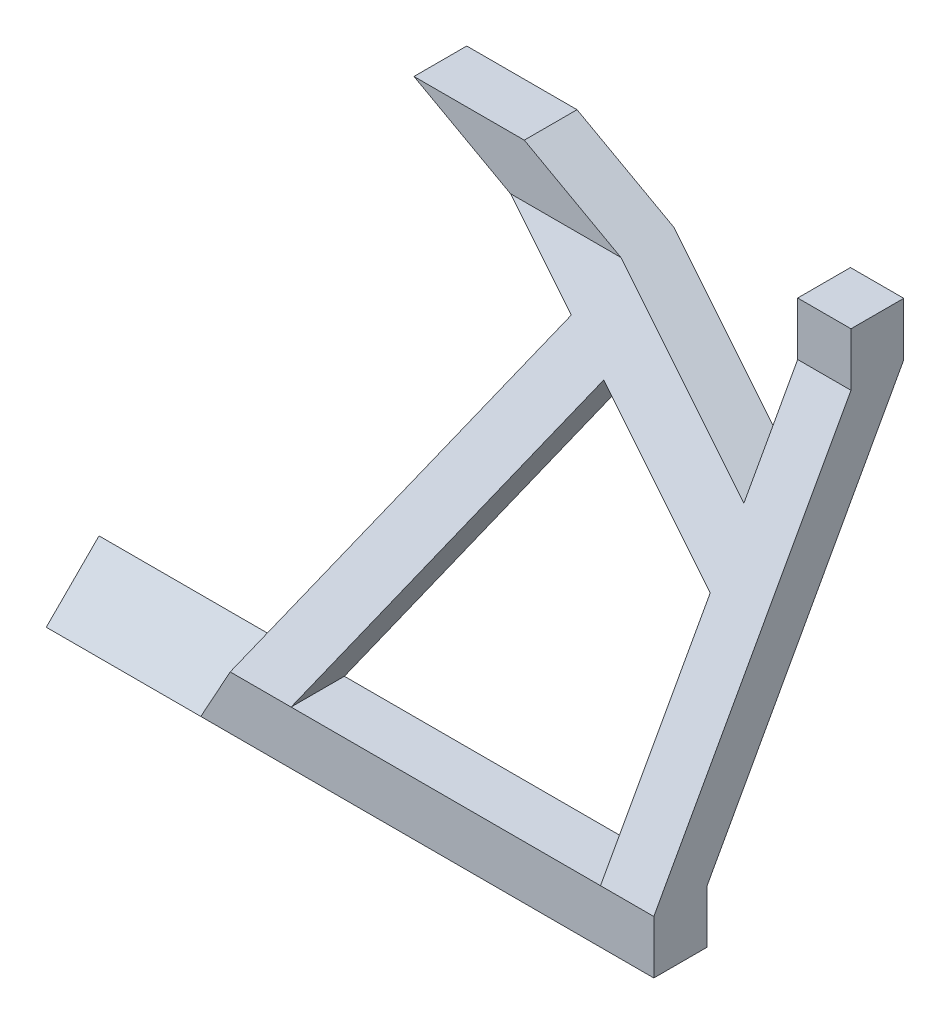
SolidWorks part; units mm, degrees
ref_plane "Płaszczyzna przednia" through (0, 0, 0) normal (0, 0, 1) x (1, 0, 0)
ref_plane "Płaszczyzna górna" through (0, 0, 0) normal (0, 1, 0) x (1, 0, 0)
ref_plane "Płaszczyzna prawa" through (0, 0, 0) normal (1, 0, 0) x (0, 0, -1)
sketch "Sketch1" plane through (0, 0, 0) normal (0, 0, 1) x (1, 0, 0)
  line L0 (99.7522, 182.6617) -> (122.7051, 97)
  line L1 (0, 0) -> (0, 300) construction
  line L2 (17.5495, 182.6617) -> (99.7522, 182.6617) construction
  line L3 (0, 239.8778) -> (60, 239.8778) construction
  line L4 (60, 239.8778) -> (80, 239.8778) construction
  line L5 (80, 239.8778) -> (80, 256.3778) construction
  line L6 (122.7051, 97) -> (122.7051, 93)
  line L7 (122.7051, 10) -> (122.7051, 0) construction
  line L8 (0, 0) -> (122.7051, 0) construction
  line L9 (109.4114, 185.2498) -> (132.7051, 98.3165)
  line L10 (122.7051, 93) -> (17.5495, 93)
  line L12 (122.7051, 87) -> (17.5495, 87)
  line L13 (80, 256.3778) -> (80, 87) construction
  line L14 (132.7051, 98.3165) -> (135.7374, 87) construction
  line L15 (143.0579, 98.3165) -> (146.0902, 87) construction
  line L16 (132.7051, 98.3165) -> (143.0579, 98.3165)
  line L17 (142.3644, 100.9047) -> (146.7917, 84.382) construction
  line L18 (143.0579, 98.3165) -> (148.0579, 98.3165) construction
  line L19 (148.0579, 98.3165) -> (148.0579, 87)
  line L20 (148.0579, 87) -> (122.7051, 87)
  line L21 (17.5495, 93) -> (17.5495, 87)
  line L22 (132.7051, 98.3165) -> (132.7051, 87) construction
  line L23 (122.7051, 97) -> (122.7051, 87) construction
  line L24 (17.5495, 93) -> (17.5495, 182.6617) construction
  line L25 (99.7522, 182.6617) -> (109.4114, 185.2498) construction
  line L30 (109.4114, 185.2498) -> (99.7522, 182.6617)
  line L31 (80, 256.3778) -> (122.7051, 97) construction
  line L32 (109.4114, 185.2498) -> (114.2411, 186.5439)
  line L33 (109.4114, 185.2498) -> (110.7055, 180.4202)
  line L34 (110.7055, 180.4202) -> (115.5352, 181.7143)
  line L35 (114.2411, 186.5439) -> (115.5352, 181.7143)
  line L36 (109.4114, 185.2498) -> (115.5352, 181.7143) construction
  line L37 (110.7055, 180.4202) -> (114.2411, 186.5439) construction
  line L38 (89.6593, 258.966) -> (132.7051, 98.3165) construction
  line L39 (132.7051, 98.3165) -> (137.1324, 81.7938) construction
  line L40 (122.7051, 93) -> (122.7051, 87) construction
  line L41 (132.7051, 87) -> (132.7051, 0)
  line L42 (132.7051, 87) -> (132.7051, 98.3165) construction
  line L44 (47.7051, 0) -> (132.7051, 0)
  line L49 (50.7051, 87) -> (85.2065, 67.9623)
  line L50 (122.7051, 47.2707) -> (122.7051, 10)
  line L52 (71.4037, 87) -> (122.7051, 58.692)
  line L53 (122.7051, 47.2707) -> (109.5023, 47.2707) construction
  line L56 (70.1733, 10) -> (40.8607, 10) construction
  line L57 (93.962, 63.131) -> (122.7051, 47.2707)
  line L58 (122.7051, 58.692) -> (122.7051, 87)
  line L59 (50.7051, 93) -> (50.7051, 87) construction
  line L60 (85.2065, 67.9623) -> (47.7051, 0)
  line L61 (122.7051, 10) -> (64.6445, 10)
  line L62 (64.6445, 10) -> (93.962, 63.131)
  line L63 (47.7051, 0) -> (40.8607, 0)
  line L64 (40.8607, 0) -> (50.7051, 87)
  arc A0 (143.0579, 98.3165) -> (148.0579, 98.3165) centre (145.5579, 98.3165) cw
  point P3 (17.5495, 177.6617)
  point P31 (112.4733, 183.4821)
  point P32 (122.7051, 90)
  dimension "D16" = 2.5
  dimension "D1" = 60
  dimension "D2" = 20
  dimension "D3" = 16.5
  dimension "D4" = 15
  dimension "D5" = 165
  dimension "D6" = 10
  dimension "D7" = 90
  dimension "D9" = 10
  dimension "D10" = 90
  dimension "D11" = 5
  dimension "D12" = 6
  dimension "D13" = 300
  dimension "D14" = 105.1556
  dimension "D15" = 5
  dimension "D17" = 182.6617
  dimension "D18" = 10
  dimension "D19" = 85
  dimension "D22" = 115.1556
  dimension "D23" = 82
  dimension "D20" = 10
  dimension "D24" = 10
  dimension "D25" = 10
  dimension "D26" = 16.9393
  dimension "D27" = 10
  dimension "D8" = 10
sketch "Sketch8" plane through (0, 0, 0) normal (0, 1, 0) x (1, 0, 0)
  line L0 (0, 0) -> (0, -64.45) construction
  line L1 (0, -64.45) -> (47.7051, -64.45) construction
  line L2 (47.7051, -74.45) -> (132.7051, -74.45)
  line L3 (47.7051, -74.45) -> (47.7051, -64.45)
  line L4 (47.7051, -64.45) -> (132.7051, -64.45)
  line L5 (132.7051, -74.45) -> (132.7051, -64.45)
  line L6 (47.7051, -74.45) -> (132.7051, -64.45) construction
  line L7 (47.7051, -64.45) -> (132.7051, -74.45) construction
  line L8 (47.7051, 0) -> (47.7051, -27.1481) construction
  line L9 (132.7051, 0) -> (132.7051, -19.275) construction
  point P7 (90.2051, -69.45)
  point P15 (49.6421, -64)
  dimension "D1" = 64.45
  dimension "D2" = 10
extrude "Boss-Extrude4" add sketch "Sketch8" along normal blind 10
ref_plane "Plane5" through (0, 87, 0) normal (0, 1, 0) x (1, 0, 0)
sketch "Sketch9" plane through (0, 87, 0) normal (0, 1, 0) x (1, 0, 0)
  line L0 (50.7051, -37.45) -> (132.7051, -37.45) construction
  line L1 (50.7051, 0) -> (50.7051, -37.45) construction
  line L2 (132.7051, 0) -> (132.7051, -37.45) construction
  line L4 (50.7051, -37.45) -> (132.7051, -37.45)
  line L5 (50.7051, -37.45) -> (50.7051, -27.55)
  line L6 (50.7051, -27.55) -> (132.7051, -27.55)
  line L7 (132.7051, -37.45) -> (132.7051, -27.55)
  line L8 (50.7051, -37.45) -> (132.7051, -27.55) construction
  line L9 (50.7051, -27.55) -> (132.7051, -37.45) construction
  point P12 (91.7051, -32.5)
  dimension "D1" = 37.45
  dimension "D2" = 9.9
extrude "Boss-Extrude5" add sketch "Sketch9" against normal blind 10 separate body
loft "Loft1" add section face at (91.7051, 77, 32.5) section face at (90.2051, 10, 69.45)
extrude "Cut-Extrude2" cut sketch "Sketch1" against normal through all both and the other way through all contours L52 L58 L12 | L62 L61 L50 L57 | L63 L64 L49 L60
sketch "Sketch10" plane through (132.7051, 0, 0) normal (1, 0, 0) x (0, 0, -1)
  line L0 (-64.55, 9.9) -> (-64.55, 0)
  line L1 (-64.55, 0) -> (-74.45, 0)
  line L2 (-74.45, 0) -> (-64.55, 9.9)
  dimension "D1" = 9.9
  dimension "D2" = 9.9
extrude "Boss-Extrude6" add sketch "Sketch10" against normal blind 114
